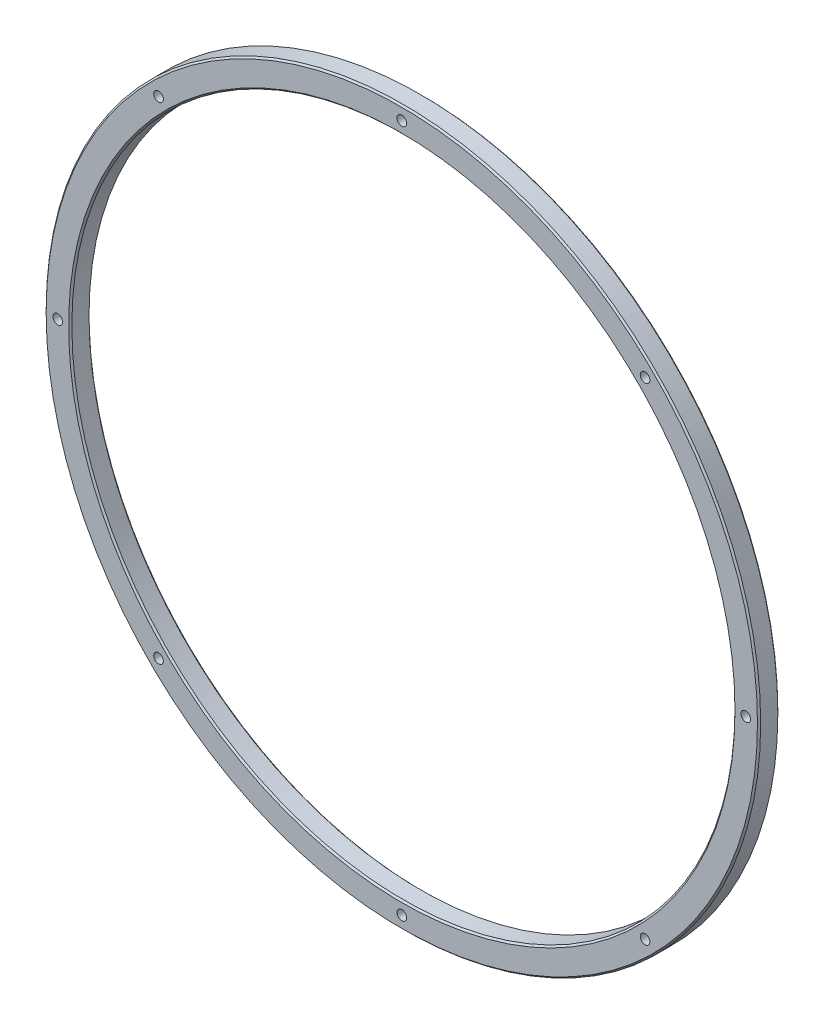
SolidWorks part; units mm, degrees
material "Polyetheretherketone (PEEK)"
ref_plane "Front Plane" through (0, 0, 0) normal (0, 0, 1) x (1, 0, 0)
ref_plane "Top Plane" through (0, 0, 0) normal (0, 1, 0) x (1, 0, 0)
ref_plane "Right Plane" through (0, 0, 0) normal (1, 0, 0) x (0, 0, -1)
sketch "Sketch1" plane through (0, 0, 0) normal (0, 0, 1) x (1, 0, 0)
  circle A0 centre (0, 0) radius 111.25
  circle A1 centre (0, 0) radius 103.25
  dimension "D1" = 206.5
  dimension "D2" = 222.5
extrude "Extrude1" add sketch "Sketch1" along normal blind 6.35
hole_wizard "M3x0.5 Tapped Hole1" positions "Sketch5" profile "Sketch6" tap size "M3x0.5" standard "Ansi Metric" end condition through all
sketch "Sketch5" plane through (0, 0, 6.35) normal (0, 0, 1) x (1, 0, 0)
  point P0 (0, 107.125)
  dimension "D1" = 107.125
sketch "Sketch6" plane through (0, 107.125, 6.35) normal (1, 0, 0) x (0, -1, 0)
  line L0 (0, 0) -> (0, 6.35)
  line L1 (0, 6.35) -> (1.5, 6.35)
  line L2 (1.5, 6.35) -> (1.5, 0)
  line L5 (1.5, 0) -> (0, 0)
  line L11 (0, -6.35) -> (0, 107.95) construction
  dimension "Thread Major Dia." = 3
  dimension "Thru Tap Drill Depth" = 6.35
pattern_circular "CirPattern1" count 8 over 360 about axis through (0, 0, 0) along (0, 0, 1) of "M3x0.5 Tapped Hole1"
chamfer "Chamfer1" distance 0.5 angle 45 4 edges at (103.25, 0, 0) (111.25, 0, 0) (103.25, 0, 6.35) (111.25, 0, 6.35)
hole_wizard "#10-24 Tapped Hole1" positions "Sketch8" profile "Sketch9" tap size "#10-24" standard "Ansi Inch"
sketch "Sketch8" plane through (0, 0, 0) normal (0, 0, -1) x (-1, 0, 0)
  line L0 (0, 0) -> (75.7488, 75.7488) construction
  line L2 (70.1521, 81.3456) -> (81.3456, 70.1521) construction
  circle A1 centre (75.7488, 75.7488) radius 1.5 construction
  point P0 (70.1521, 81.3456)
  point P18 (81.3456, 70.1521)
  dimension "D1" = 15.83
sketch "Sketch9" plane through (-70.1521, 81.3456, 0) normal (1, 0, 0) x (0, 1, 0)
  line L0 (0, 0) -> (0, 6.35)
  line L1 (0, 6.35) -> (1.8986, 6.35)
  line L2 (1.8986, 6.35) -> (1.8986, 0)
  line L5 (1.8986, 0) -> (0, 0)
  line L11 (0, -6.35) -> (0, 107.95) construction
  dimension "Thru Tap Drill Dia." = 3.7973
  dimension "Thru Tap Drill Depth" = 6.35
cosmetic thread "Hole Thread1" [suppressed] parameters "D2"=4.826
cosmetic thread "Hole Thread2" [suppressed] parameters "D2"=4.826
pattern_circular "CirPattern2" [suppressed] count 4 over 360
